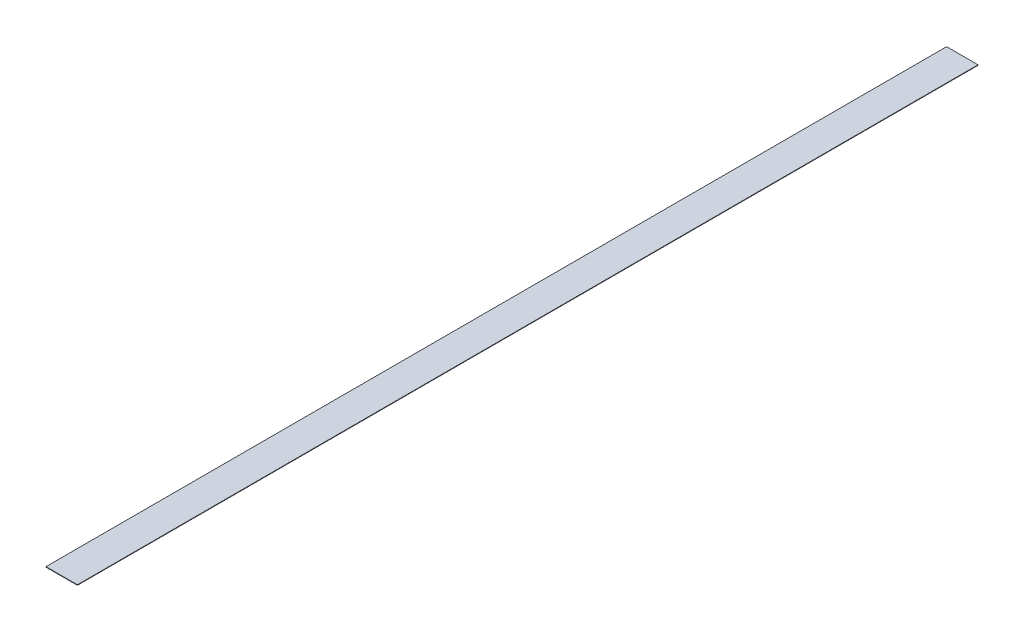
SolidWorks part; units mm, degrees
material "Silicon Rubber"
ref_plane "Front Plane" through (0, 0, 0) normal (0, 0, 1) x (1, 0, 0)
ref_plane "Top Plane" through (0, 0, 0) normal (0, 1, 0) x (1, 0, 0)
ref_plane "Right Plane" through (0, 0, 0) normal (1, 0, 0) x (0, 0, -1)
sketch "Sketch1" plane through (0, 0, 0) normal (0, 1, 0) x (1, 0, 0)
  line L1 (-25.4, 728.6625) -> (25.4, 728.6625)
  line L2 (-25.4, 728.6625) -> (-25.4, -728.6625)
  line L3 (-25.4, -728.6625) -> (25.4, -728.6625)
  line L4 (25.4, 728.6625) -> (25.4, -728.6625)
  line L5 (-25.4, 728.6625) -> (25.4, -728.6625) construction
  line L6 (-25.4, -728.6625) -> (25.4, 728.6625) construction
  point P0 (0, 0)
  dimension "D1" = 50.8
  dimension "D2" = 1457.325
extrude "Boss-Extrude1" add sketch "Sketch1" along normal blind 0.7937
